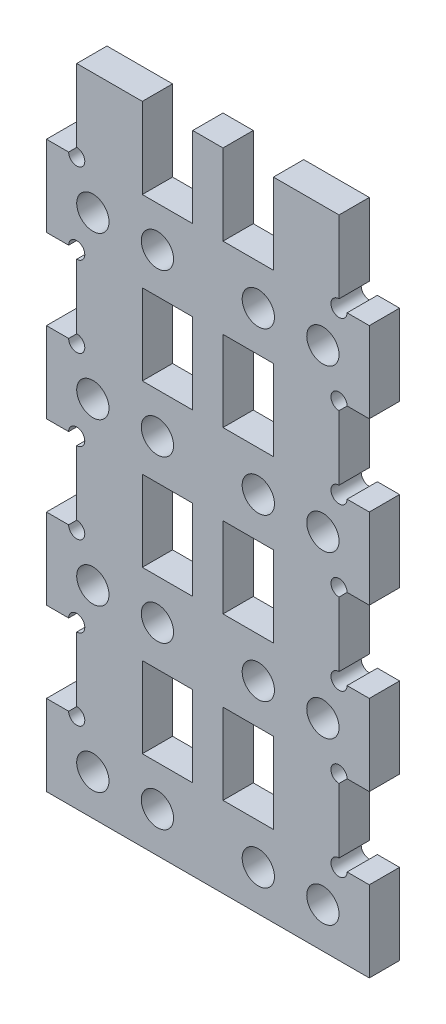
SolidWorks part; units mm, degrees
material "Thornel Mat VMA"
ref_plane "前视基准面" through (0, 0, 0) normal (0, 0, 1) x (1, 0, 0)
ref_plane "上视基准面" through (0, 0, 0) normal (0, 1, 0) x (1, 0, 0)
ref_plane "右视基准面" through (0, 0, 0) normal (1, 0, 0) x (0, 0, -1)
sketch "草图1" plane through (0, 0, 0) normal (0, 0, 1) x (1, 0, 0)
  line L0 (0, 0) -> (0, 16.7389) construction
  line L1 (16, 0) -> (-16, 0)
  line L2 (-16, 0) -> (-16, 8)
  line L3 (-16, 8) -> (-13, 8)
  line L4 (-13, 8) -> (-13, 16)
  line L5 (-13, 16) -> (-16, 16)
  line L6 (-16, 16) -> (-16, 24)
  line L7 (-16, 24) -> (-13, 24)
  line L8 (-13, 24) -> (-13, 32)
  line L9 (-13, 32) -> (-16, 32)
  line L10 (-16, 32) -> (-16, 40)
  line L11 (-16, 40) -> (-13, 40)
  line L12 (-13, 40) -> (-13, 48)
  line L13 (-13, 48) -> (-16, 48)
  line L14 (-16, 48) -> (-16, 56)
  line L15 (-16, 56) -> (-13, 56)
  line L16 (16, 0) -> (16, 8)
  line L17 (16, 8) -> (13, 8)
  line L18 (13, 8) -> (13, 16)
  line L19 (13, 16) -> (16, 16)
  line L20 (16, 16) -> (16, 24)
  line L21 (16, 24) -> (13, 24)
  line L22 (13, 24) -> (13, 32)
  line L23 (13, 32) -> (16, 32)
  line L24 (16, 32) -> (16, 40)
  line L25 (16, 40) -> (13, 40)
  line L26 (13, 40) -> (13, 48)
  line L27 (13, 48) -> (16, 48)
  line L28 (16, 48) -> (16, 56)
  line L29 (-13, 56) -> (-13, 64)
  line L30 (-13, 64) -> (13, 64)
  line L31 (13, 56) -> (13, 64)
  line L32 (13, 56) -> (16, 56)
  point P32 (0, 56)
  point P36 (0, 64)
  dimension "D1" = 16
  dimension "D2" = 8
  dimension "D3" = 3
  dimension "D4" = 8
  dimension "D5" = 8
  dimension "D6" = 8
  dimension "D7" = 8
  dimension "D8" = 3
  dimension "D9" = 8
  dimension "D10" = 8
  dimension "D11" = 16
  dimension "D12" = 8
extrude "凸台-拉伸1" add sketch "草图1" along normal blind 3
sketch "草图2" plane through (0, 0, 3) normal (0, 0, 1) x (1, 0, 0)
  line L0 (-13, 12) -> (13, 12) construction
  line L1 (-13, 16) -> (-13, 8) construction
  line L2 (13, 8) -> (13, 16) construction
  line L3 (-13, 28) -> (13, 28) construction
  line L4 (-13, 32) -> (-13, 24) construction
  line L5 (13, 24) -> (13, 32) construction
  line L6 (-13, 44) -> (13, 44) construction
  line L7 (-13, 48) -> (-13, 40) construction
  line L8 (13, 40) -> (13, 48) construction
  line L9 (-6.5, 32) -> (-1.5, 32)
  line L10 (-6.5, 16) -> (-1.5, 16)
  line L11 (-6.5, 16) -> (-6.5, 8)
  line L12 (-6.5, 8) -> (-1.5, 8)
  line L13 (-1.5, 16) -> (-1.5, 8)
  line L14 (-6.5, 16) -> (-1.5, 8) construction
  line L15 (-6.5, 8) -> (-1.5, 16) construction
  line L16 (-6.5, 32) -> (-6.5, 24)
  line L17 (-1.5, 32) -> (-1.5, 24)
  line L18 (-6.5, 24) -> (-1.5, 24)
  line L19 (6.5, 24) -> (1.5, 24)
  line L20 (6.5, 32) -> (6.5, 24)
  line L21 (6.5, 32) -> (1.5, 32)
  line L22 (1.5, 32) -> (1.5, 24)
  line L23 (0, 12) -> (0, 19.1819) construction
  line L24 (-6.5, 48) -> (-1.5, 48)
  line L25 (-6.5, 48) -> (-6.5, 40)
  line L26 (-1.5, 48) -> (-1.5, 40)
  line L27 (-6.5, 40) -> (-1.5, 40)
  line L28 (6.5, 40) -> (1.5, 40)
  line L29 (6.5, 48) -> (6.5, 40)
  line L30 (6.5, 48) -> (1.5, 48)
  line L31 (1.5, 48) -> (1.5, 40)
  line L32 (6.5, 8) -> (1.5, 8)
  line L33 (6.5, 16) -> (6.5, 8)
  line L34 (1.5, 16) -> (1.5, 8)
  line L35 (6.5, 16) -> (1.5, 16)
  line L36 (0, 44) -> (0, 64) construction
  line L37 (13, 64) -> (-13, 64) construction
  line L38 (0, 60) -> (-4, 60) construction
  line L39 (6.5, 56) -> (1.5, 56)
  line L40 (-6.5, 64) -> (-1.5, 64)
  line L41 (-6.5, 64) -> (-6.5, 56)
  line L42 (-6.5, 56) -> (-1.5, 56)
  line L43 (-1.5, 64) -> (-1.5, 56)
  line L44 (-6.5, 64) -> (-1.5, 56) construction
  line L45 (-6.5, 56) -> (-1.5, 64) construction
  line L46 (1.5, 64) -> (1.5, 56)
  line L47 (6.5, 64) -> (1.5, 64)
  line L48 (6.5, 64) -> (6.5, 56)
  point P18 (0, 12)
  point P19 (0, 28)
  point P20 (0, 44)
  point P21 (-4, 12)
  point P53 (0, 60)
  dimension "D1" = 4
  dimension "D2" = 8
  dimension "D3" = 5
  dimension "D4" = 3
  dimension "D5" = 4
  dimension "D6" = 4
  dimension "D7" = 8
  dimension "D8" = 5
extrude "切除-拉伸1" cut sketch "草图2" against normal blind 3
sketch "草图3" plane through (0, 0, 3) normal (0, 0, 1) x (1, 0, 0)
  line L0 (-16, 4) -> (16, 4) construction
  line L1 (-16, 8) -> (-16, 0) construction
  line L2 (16, 0) -> (16, 8) construction
  line L3 (0, 4) -> (0, 12.4627) construction
  line L4 (-16, 20) -> (16, 20) construction
  line L5 (-16, 24) -> (-16, 16) construction
  line L6 (16, 16) -> (16, 24) construction
  circle A0 centre (-11.4, 4) radius 1.6
  circle A1 centre (11.4, 4) radius 1.6
  circle A2 centre (-11.4, 20) radius 1.6
  circle A3 centre (11.4, 20) radius 1.6
  circle A4 centre (-11.4, 36) radius 1.6
  circle A5 centre (11.4, 36) radius 1.6
  circle A6 centre (-11.4, 52) radius 1.6
  circle A7 centre (11.4, 52) radius 1.6
  point P6 (0, 4)
  point P7 (-11.4, 4)
  dimension "D2" = 3.2
  dimension "D1" = 11.4
  dimension "D3" = 4
extrude "切除-拉伸2" cut sketch "草图3" against normal blind 3
sketch "草图5" plane through (0, 0, 3) normal (0, 0, 1) x (1, 0, 0)
  line L0 (0, 0) -> (0, 8.6586) construction
  line L1 (-16, 0) -> (16, 0) construction
  line L2 (-11.4, 4) -> (0, 4) construction
  circle A0 centre (-5, 4) radius 1.6
  circle A1 centre (5, 4) radius 1.6
  circle A2 centre (-5, 20) radius 1.6
  circle A3 centre (5, 20) radius 1.6
  circle A4 centre (-5, 36) radius 1.6
  circle A5 centre (5, 36) radius 1.6
  circle A6 centre (-5, 52) radius 1.6
  circle A7 centre (5, 52) radius 1.6
  point P7 (-5, 4)
  dimension "D2" = 3.2
  dimension "D1" = 5
  dimension "D3" = 4
extrude "切除-拉伸3" cut sketch "草图5" against normal up to next
sketch "草图6" plane through (0, 0, 3) normal (0, 0, 1) x (1, 0, 0)
  line L0 (0, 0) -> (0, 18.1911) construction
  circle A0 centre (-13, 8) radius 0.8
  circle A1 centre (-13, 16) radius 0.8
  circle A2 centre (-13, 24) radius 0.8
  circle A3 centre (-13, 32) radius 0.8
  circle A4 centre (-13, 40) radius 0.8
  circle A5 centre (-13, 48) radius 0.8
  circle A6 centre (-13, 56) radius 0.8
  circle A7 centre (13, 8) radius 0.8
  circle A8 centre (-13, 64) radius 0.8 [skipped]
  circle A9 centre (13, 16) radius 0.8
  circle A10 centre (13, 24) radius 0.8
  circle A11 centre (13, 32) radius 0.8
  circle A12 centre (13, 40) radius 0.8
  circle A13 centre (13, 48) radius 0.8
  circle A14 centre (13, 56) radius 0.8
  dimension "D1" = 1.6
  dimension "D2" = 1.6
  dimension "D3" = 4
extrude "切除-拉伸4" cut sketch "草图6" against normal up to next
